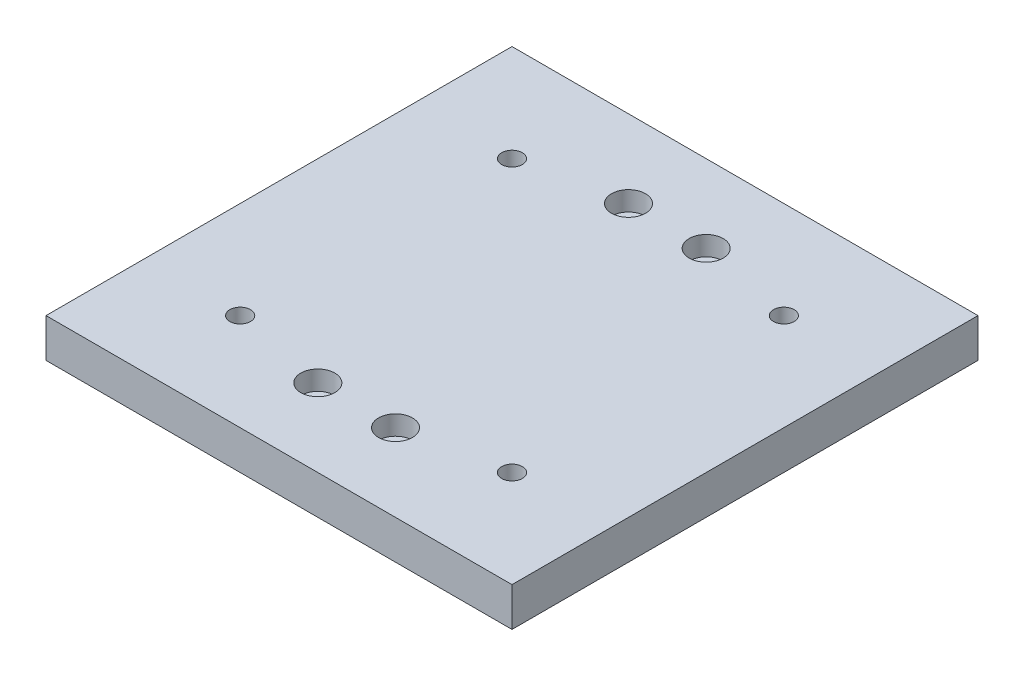
SolidWorks part; units mm, degrees
ref_plane "Front Plane" through (0, 0, 0) normal (0, 0, 1) x (1, 0, 0)
ref_plane "Top Plane" through (0, 0, 0) normal (0, 1, 0) x (1, 0, 0)
ref_plane "Right Plane" through (0, 0, 0) normal (1, 0, 0) x (0, 0, -1)
sketch "Sketch1" plane through (0, 0, 0) normal (0, 1, 0) x (1, 0, 0)
  line L1 (76.2, 76.2) -> (-76.2, 76.2)
  line L2 (76.2, 76.2) -> (76.2, -76.2)
  line L3 (76.2, -76.2) -> (-76.2, -76.2)
  line L4 (-76.2, 76.2) -> (-76.2, -76.2)
  line L5 (76.2, 76.2) -> (-76.2, -76.2) construction
  line L6 (76.2, -76.2) -> (-76.2, 76.2) construction
  point P0 (0, 0)
  dimension "D1" = 152.4
  dimension "D2" = 152.4
extrude "Boss-Extrude1" add sketch "Sketch1" along normal blind 12.7
ref_point "Point1"
ref_plane "Plane1" through (0, 0, 0) normal (0, 0, 1) x (1, 0, 0)
ref_plane "Plane2" through (0, 0, 0) normal (-1, 0, 0) x (0, 0, 1)
hole_wizard "CBORE for 1/4 Socket Head Cap Screw1" positions "Sketch4" profile "Sketch5" counterbore size "1/4" standard "ANSI Inch" end condition through all
sketch "Sketch4" plane through (0, 12.7, 0) normal (0, 1, 0) x (1, 0, 0)
  line L1 (-6.985, 0) -> (6.985, 0) construction
  line L2 (0, 6.985) -> (0, -6.985) construction
  point P0 (-12.7, -50.8)
  point P14 (12.7, -50.8)
  point P15 (12.7, 50.8)
  point P16 (-12.7, 50.8)
  dimension "D1" = 12.7
  dimension "D2" = 50.8
sketch "Sketch5" plane through (-12.7, 12.7, 50.8) normal (1, 0, 0) x (0, 0, 1)
  line L0 (0, 0) -> (0, 12.7)
  line L1 (0, 12.7) -> (3.3782, 12.7)
  line L3 (3.3782, 12.7) -> (3.3782, 6.35)
  line L4 (3.3782, 6.35) -> (5.5562, 6.35)
  line L5 (5.5562, 6.35) -> (5.5563, 0)
  line L7 (5.5563, 0) -> (0, 0)
  line L11 (0, -6.35) -> (0, 107.95) construction
  dimension "Thru Hole Dia." = 6.7564
  dimension "Thru Hole Depth" = 12.7
  dimension "C'Bore Dia." = 11.1125
  dimension "C'Bore Depth" = 6.35
hole_wizard "CBORE for 1/4 Socket Head Cap Screw2" positions "Sketch6" profile "Sketch7" counterbore size "1/4" standard "ANSI Inch" end condition through all
sketch "Sketch6" plane through (0, 0, 0) normal (0, -1, 0) x (-1, 0, 0)
  line L1 (-6.985, 0) -> (6.985, 0) construction
  line L2 (0, -6.985) -> (0, 6.985) construction
  point P0 (-44.45, -44.45)
  point P7 (-44.45, 44.45)
  point P10 (44.45, 44.45)
  point P11 (44.45, -44.45)
  dimension "D1" = 44.45
  dimension "D2" = 44.45
sketch "Sketch7" plane through (44.45, 0, 44.45) normal (1, 0, 0) x (0, 0, -1)
  line L0 (0, 0) -> (0, 12.7)
  line L1 (0, 12.7) -> (3.3782, 12.7)
  line L3 (3.3782, 12.7) -> (3.3782, 6.35)
  line L4 (3.3782, 6.35) -> (5.5562, 6.35)
  line L5 (5.5562, 6.35) -> (5.5563, 0)
  line L7 (5.5563, 0) -> (0, 0)
  line L11 (0, -6.35) -> (0, 107.95) construction
  dimension "Thru Hole Dia." = 6.7564
  dimension "Thru Hole Depth" = 12.7
  dimension "C'Bore Dia." = 11.1125
  dimension "C'Bore Depth" = 6.35
